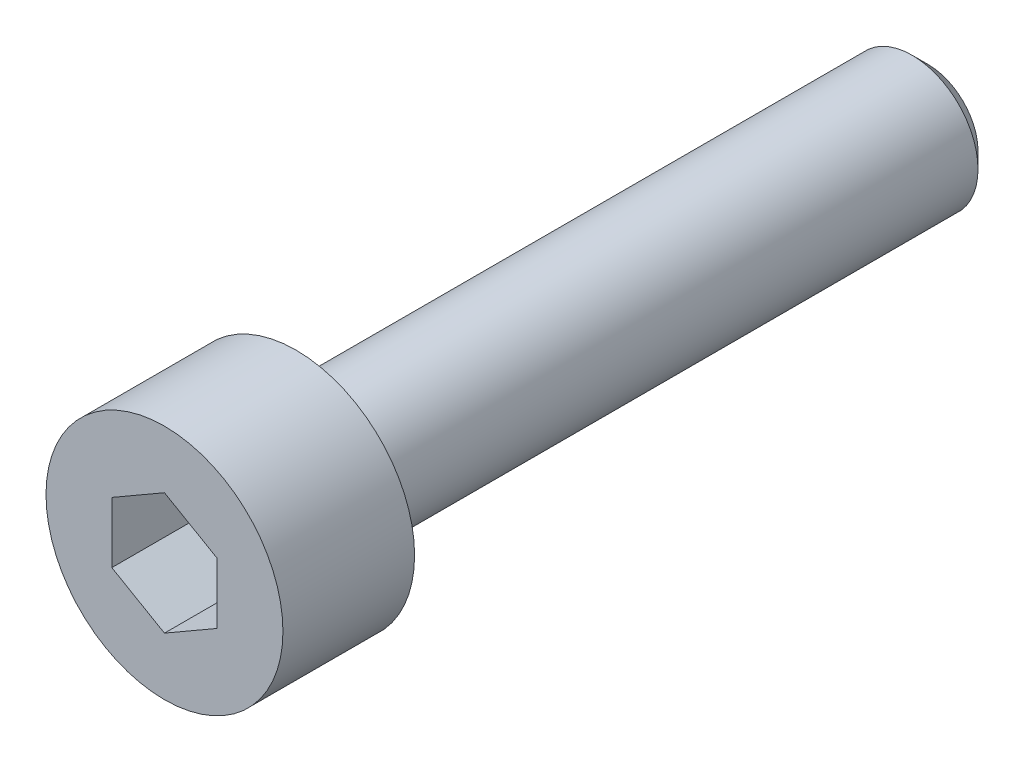
SolidWorks part; units mm, degrees
ref_plane "Front Plane" through (0, 0, 0) normal (0, 0, 1) x (1, 0, 0)
ref_plane "Top Plane" through (0, 0, 0) normal (0, 1, 0) x (1, 0, 0)
ref_plane "Right Plane" through (0, 0, 0) normal (1, 0, 0) x (0, 0, -1)
sketch "Sketch1" plane through (0, 0, 0) normal (0, 0, 1) x (1, 0, 0)
  circle A0 centre (0, 0) radius 2.25
  dimension "D1" = 4.5
extrude "Boss-Extrude1" add sketch "Sketch1" along normal blind 2.5
sketch "Sketch2" plane through (0, 0, 0) normal (0, 0, -1) x (-1, 0, 0)
  circle A0 centre (0, 0) radius 1.25
  dimension "D1" = 2.5
extrude "Boss-Extrude2" add sketch "Sketch2" along normal blind 12
chamfer "Chamfer1" distance 0.3 angle 45 1 edges at (-1.25, 0, -12)
sketch "Sketch3" plane through (0, 0, 2.5) normal (0, 0, 1) x (1, 0, 0)
  line L1 (0, 1.1547) -> (-1, 0.5774)
  line L2 (-1, 0.5774) -> (-1, -0.5774)
  line L3 (-1, -0.5774) -> (0, -1.1547)
  line L4 (0, -1.1547) -> (1, -0.5774)
  line L5 (1, -0.5774) -> (1, 0.5774)
  line L6 (1, 0.5774) -> (0, 1.1547)
  circle A0 centre (0, 0) radius 1 construction
  dimension "D1" = 2
extrude "Cut-Extrude1" cut sketch "Sketch3" against normal blind 2
